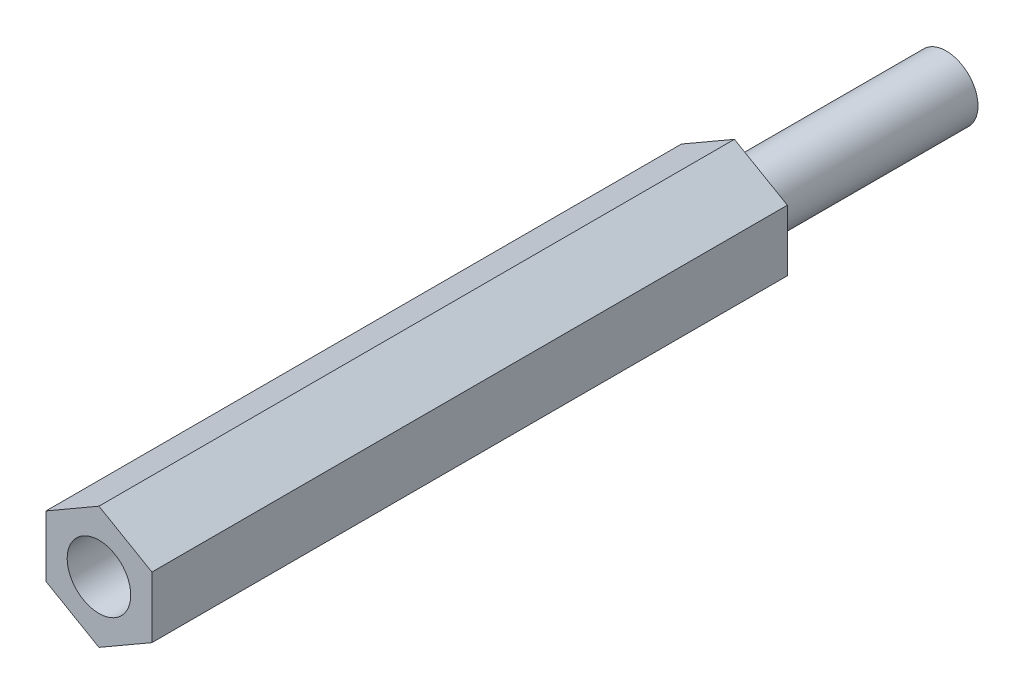
SolidWorks part; units mm, degrees
ref_plane "Plan de face" through (0, 0, 0) normal (0, 0, 1) x (1, 0, 0)
ref_plane "Plan de dessus" through (0, 0, 0) normal (0, 1, 0) x (1, 0, 0)
ref_plane "Plan de droite" through (0, 0, 0) normal (1, 0, 0) x (0, 0, -1)
sketch "Esquisse1" plane through (0, 0, 0) normal (0, 0, 1) x (1, 0, 0)
  line L1 (0, -2.8868) -> (2.5, -1.4434)
  line L2 (2.5, -1.4434) -> (2.5, 1.4434)
  line L3 (2.5, 1.4434) -> (0, 2.8868)
  line L4 (0, 2.8868) -> (-2.5, 1.4434)
  line L5 (-2.5, 1.4434) -> (-2.5, -1.4434)
  line L6 (-2.5, -1.4434) -> (0, -2.8868)
  circle A0 centre (0, 0) radius 2.5 construction
  circle A1 centre (0, 0) radius 1.5
  dimension "D1" = 3
  dimension "D2" = 5
extrude "Boss.-Extru.2" add sketch "Esquisse1" along normal blind 30 contours A1 | L1 L2 L3 L4 L5 L6
sketch "Esquisse3" plane through (0, 0, 0) normal (0, 0, -1) x (-1, 0, 0)
  circle A0 centre (0, 0) radius 1.5
extrude "Boss.-Extru.3" add sketch "Esquisse3" against normal blind 20 and the other way blind 10
